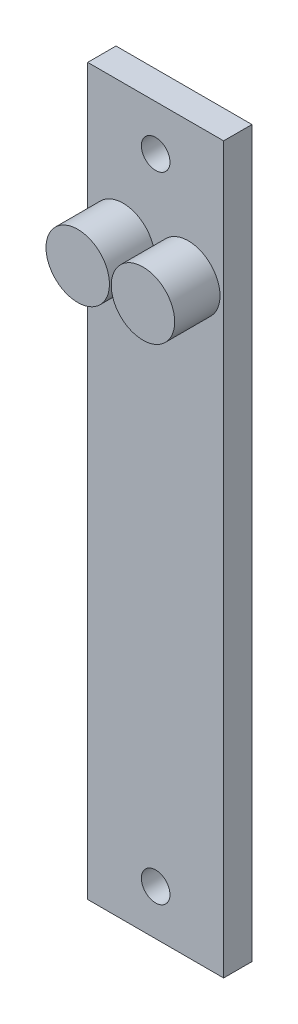
SolidWorks part; units mm, degrees
ref_plane "Front Plane" through (0, 0, 0) normal (0, 0, 1) x (1, 0, 0)
ref_plane "Top Plane" through (0, 0, 0) normal (0, 1, 0) x (1, 0, 0)
ref_plane "Right Plane" through (0, 0, 0) normal (1, 0, 0) x (0, 0, -1)
sketch "Sketch1" plane through (0, 0, 0) normal (0, 0, 1) x (1, 0, 0)
  line L1 (-19.05, 101.6) -> (19.05, 101.6)
  line L2 (-19.05, 101.6) -> (-19.05, -101.6)
  line L3 (-19.05, -101.6) -> (19.05, -101.6)
  line L4 (19.05, 101.6) -> (19.05, -101.6)
  dimension "D1" = 38.1
  dimension "D2" = 19.05
  dimension "D3" = 203.2
  dimension "D4" = 101.6
extrude "Boss-Extrude1" add sketch "Sketch1" along normal blind 7.9375
hole_wizard "O (0.316) Diameter Hole1" positions "Sketch3" profile "Sketch2" hole size "O" standard "ANSI Inch" end condition through all
sketch "Sketch3" plane through (0, 0, 7.9375) normal (0, 0, 1) x (1, 0, 0)
  point P0 (0, 88.9)
  dimension "D1" = 88.9
sketch "Sketch2" plane through (0, 88.9, 7.9375) normal (1, 0, 0) x (0, -1, 0)
  line L0 (0, 0) -> (0, 7.9375)
  line L1 (0, 7.9375) -> (4.0132, 7.9375)
  line L2 (4.0132, 7.9375) -> (4.0132, 0)
  line L5 (4.0132, 0) -> (0, 0)
  line L11 (0, -6.35) -> (0, 107.95) construction
  dimension "Thru Hole Dia." = 8.0264
  dimension "Thru Hole Depth" = 7.9375
mirror "Mirror1" about plane through (0, 0, 0) normal (0, 1, 0) of "O (0.316) Diameter Hole1"
sketch "Sketch4" plane through (0, 0, 7.9375) normal (0, 0, 1) x (1, 0, 0)
  line L0 (19.05, -101.6) -> (19.05, 101.6) construction
  line L1 (-19.05, 101.6) -> (-19.05, -101.6) construction
  line L2 (19.05, 101.6) -> (-19.05, 101.6) construction
  circle A0 centre (-9.144, 63.5) radius 8.89
  circle A1 centre (9.144, 63.5) radius 8.89
  dimension "D2" = 17.78
  dimension "D4" = 17.78
  dimension "D1" = 9.906
  dimension "D3" = 9.906
  dimension "D5" = 38.1
  dimension "D6" = 38.1
extrude "Boss-Extrude2" add sketch "Sketch4" along normal blind 12.7
equation "\"D2@Sketch1\"=\"D1@Sketch1\"/2"
equation "\"D4@Sketch1\"=\"D3@Sketch1\"/2"
equation "\"D3@Sketch4\"=\"D1@Sketch4\""
equation "\"D4@Sketch4\"=\"D2@Sketch4\""
equation "\"D6@Sketch4\"=\"D5@Sketch4\""
